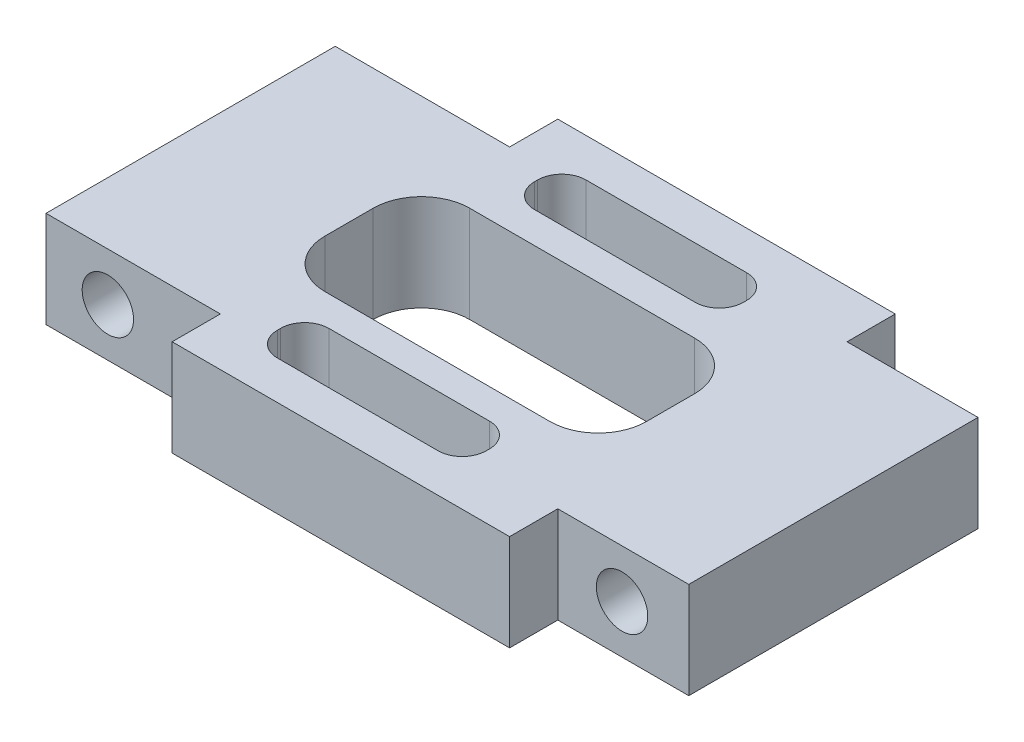
SolidWorks part; units mm, degrees
ref_plane "Спереди" through (0, 0, 0) normal (0, 0, 1) x (1, 0, 0)
ref_plane "Сверху" through (0, 0, 0) normal (0, 1, 0) x (1, 0, 0)
ref_plane "Справа" through (0, 0, 0) normal (1, 0, 0) x (0, 0, -1)
sketch "Эскиз1" plane through (0, 0, 0) normal (0, 1, 0) x (1, 0, 0)
  line L0 (-9.65, 9) -> (-9.65, 12)
  line L1 (-20.5, 0) -> (19.5, 0) construction
  line L2 (19.5, -9) -> (19.5, 9)
  line L3 (-20.5, 8) -> (19.5, 8) construction
  line L4 (-20.5, -9) -> (-20.5, 9)
  line L5 (19.5, -9) -> (-20.5, 9) construction
  line L6 (19.5, 9) -> (-20.5, -9) construction
  line L7 (-9.65, 12) -> (11.35, 12)
  line L8 (11.35, 12) -> (11.35, 9)
  line L9 (11.35, 9) -> (19.5, 9)
  line L10 (-20.5, -9) -> (-9.65, -9)
  line L11 (-9.65, -9) -> (-9.65, -12)
  line L12 (-9.65, -12) -> (11.35, -12)
  line L13 (11.35, -12) -> (11.35, -9)
  line L14 (11.35, -9) -> (19.5, -9)
  line L15 (-9.65, 9) -> (-20.5, 9)
  line L16 (6.4064, -4.5421) -> (-7.5936, -4.5421)
  line L17 (9.4064, -1.5421) -> (9.4064, 1.4579)
  line L18 (6.4064, 4.4579) -> (-7.5936, 4.4579)
  line L19 (-10.5936, -1.5421) -> (-10.5936, 1.4579)
  line L20 (9.4064, -4.5421) -> (-10.5936, 4.4579) construction
  line L21 (9.4064, 4.4579) -> (-10.5936, -4.5421) construction
  line L22 (-20.5, -8) -> (19.5, -8) construction
  line L24 (4.5, 6.4) -> (-5.5, 6.4)
  line L25 (6, 7.9) -> (6, 8.1)
  line L26 (4.5, 9.6) -> (-5.5, 9.6)
  line L27 (-7, 7.9) -> (-7, 8.1)
  line L28 (6, 6.4) -> (-7, 9.6) construction
  line L29 (6, 9.6) -> (-7, 6.4) construction
  line L30 (4.5, -9.6) -> (-5.5, -9.6)
  line L31 (6, -8.1) -> (6, -7.9)
  line L32 (4.5, -6.4) -> (-5.5, -6.4)
  line L33 (-7, -8.1) -> (-7, -7.9)
  line L34 (6, -9.6) -> (-7, -6.4) construction
  line L35 (6, -6.4) -> (-7, -9.6) construction
  arc A0 (6.4064, -4.5421) -> (9.4064, -1.5421) centre (6.4064, -1.5421) ccw
  arc A1 (-7.5936, -4.5421) -> (-10.5936, -1.5421) centre (-7.5936, -1.5421) cw
  arc A2 (6.4064, 4.4579) -> (9.4064, 1.4579) centre (6.4064, 1.4579) cw
  arc A3 (-7.5936, 4.4579) -> (-10.5936, 1.4579) centre (-7.5936, 1.4579) ccw
  arc A4 (6, -7.9) -> (4.5, -6.4) centre (4.5, -7.9) ccw
  arc A5 (6, -8.1) -> (4.5, -9.6) centre (4.5, -8.1) cw
  arc A6 (-5.5, -9.6) -> (-7, -8.1) centre (-5.5, -8.1) cw
  arc A7 (-7, -7.9) -> (-5.5, -6.4) centre (-5.5, -7.9) cw
  arc A8 (6, 7.9) -> (4.5, 6.4) centre (4.5, 7.9) cw
  arc A9 (6, 8.1) -> (4.5, 9.6) centre (4.5, 8.1) ccw
  arc A10 (-5.5, 6.4) -> (-7, 7.9) centre (-5.5, 7.9) cw
  arc A11 (-5.5, 9.6) -> (-7, 8.1) centre (-5.5, 8.1) ccw
  point P0 (-0.5, 8)
  point P16 (-0.5, 0)
  point P37 (-0.5, -8)
  point P69 (0, 0)
  point P70 (-0.5, 0)
  dimension "D8" = 3
  dimension "D13" = 1.5
  dimension "D1" = 18
  dimension "D2" = 40
  dimension "D3" = 3
  dimension "D4" = 21
  dimension "D5" = 10.85
  dimension "D6" = 9
  dimension "D7" = 20
  dimension "D9" = 8
  dimension "D10" = 16
  dimension "D11" = 3.2
  dimension "D12" = 13
extrude "Бобышка-Вытянуть1" add sketch "Эскиз1" along normal blind 6
sketch "Эскиз2" plane through (0, 0, -9) normal (0, 0, -1) x (-1, 0, 0)
  line L0 (20.5, 3) -> (-19.5, 3) construction
  line L1 (20.5, 6) -> (20.5, 0) construction
  line L2 (-19.5, 6) -> (-19.5, 0) construction
  circle A0 centre (-15.35, 3) radius 1.6
  circle A1 centre (16.65, 3) radius 1.6
  dimension "D1" = 32
  dimension "D2" = 3.85
extrude "Вырез-Вытянуть1" cut sketch "Эскиз2" against normal through all
